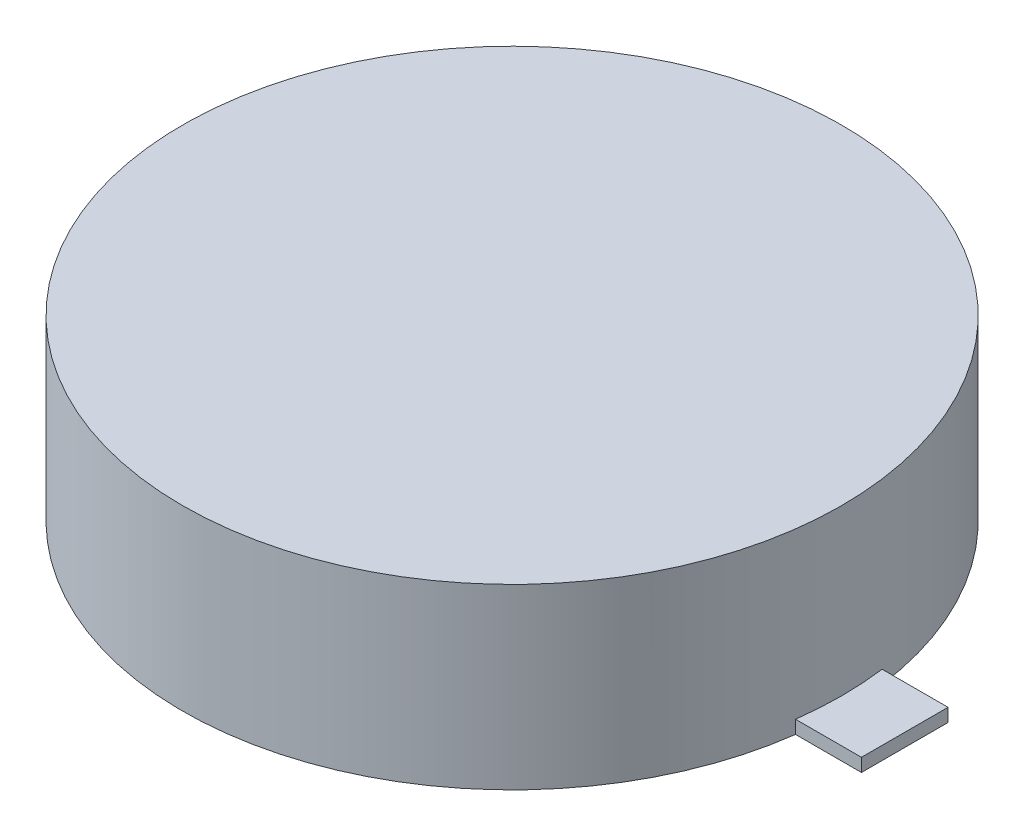
SolidWorks part; units mm, degrees
ref_plane "Front Plane" through (0, 0, 0) normal (0, 0, 1) x (1, 0, 0)
ref_plane "Top Plane" through (0, 0, 0) normal (0, 1, 0) x (1, 0, 0)
ref_plane "Right Plane" through (0, 0, 0) normal (1, 0, 0) x (0, 0, -1)
sketch "Sketch1" plane through (0, 0, 0) normal (0, 1, 0) x (1, 0, 0)
  circle A0 centre (0, 0) radius 5
  dimension "D1" = 10
extrude "Boss-Extrude1" add sketch "Sketch1" along normal blind 2.7
sketch "Sketch2" plane through (0, 0, 0) normal (0, 1, 0) x (1, 0, 0)
  line L0 (-1.485, 0) -> (1.485, 0) construction
  line L1 (4.9567, 0.6568) -> (5.9567, 0.6568)
  line L2 (4.9567, 0.6568) -> (4.9567, -0.6568)
  line L3 (4.9567, -0.6568) -> (5.9567, -0.6568)
  line L4 (5.9567, 0.6568) -> (5.9567, -0.6568)
  circle A0 centre (0, 0) radius 5 construction
  point P6 (5.9567, 0)
  dimension "D1" = 1
extrude "Boss-Extrude2" add sketch "Sketch2" along normal blind 0.2
